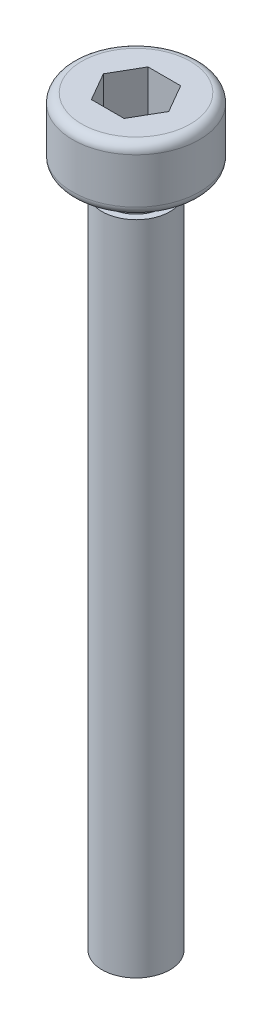
SolidWorks part; units mm, degrees
material "AISI 304"
ref_plane "前视基准面" through (0, 0, 0) normal (0, 0, 1) x (1, 0, 0)
ref_plane "上视基准面" through (0, 0, 0) normal (0, 1, 0) x (1, 0, 0)
ref_plane "右视基准面" through (0, 0, 0) normal (1, 0, 0) x (0, 0, -1)
sketch "草图1" plane through (0, 0, 0) normal (0, 0, 1) x (1, 0, 0)
  line L0 (0, 0) -> (0, 32.8) construction
  line L1 (0, 32.8) -> (-2.4, 32.8)
  line L2 (-2.8, 32.4) -> (-2.8, 30.4)
  line L3 (-2.4, 30) -> (-1.2, 30)
  line L4 (-1.2, 30) -> (-1.2, 29)
  line L5 (-1.2, 29) -> (-1.5, 29)
  line L6 (-1.5, 29) -> (-1.5, 0)
  line L7 (-1.5, 0) -> (0, 0)
  line L8 (0, 0) -> (0, 32.8)
  arc A0 (-2.8, 30.4) -> (-2.4, 30) centre (-2.4, 30.4) ccw
  arc A1 (-2.4, 32.8) -> (-2.8, 32.4) centre (-2.4, 32.4) ccw
  point P11 (-2.8, 30)
  point P14 (-2.8, 32.8)
  dimension "D7" = 0.4
  dimension "D1" = 30
  dimension "D2" = 2.8
  dimension "D3" = 5.6
  dimension "D4" = 3
  dimension "D5" = 1
  dimension "D6" = 1.2
revolve "旋转1" add sketch "草图1" angle 360 about L0
cosmetic thread "装饰螺纹线1" parameters "D2"=2.439
sketch "草图2" plane through (0, 32.8, 0) normal (0, 1, 0) x (1, 0, 0)
  line L1 (-0.7217, 1.25) -> (-1.4434, 0)
  line L2 (-1.4434, 0) -> (-0.7217, -1.25)
  line L3 (-0.7217, -1.25) -> (0.7217, -1.25)
  line L4 (0.7217, -1.25) -> (1.4434, 0)
  line L5 (1.4434, 0) -> (0.7217, 1.25)
  line L6 (0.7217, 1.25) -> (-0.7217, 1.25)
  circle A0 centre (0, 0) radius 1.25 construction
  dimension "D1" = 2.5
extrude "切除-拉伸1" cut sketch "草图2" against normal blind 2
